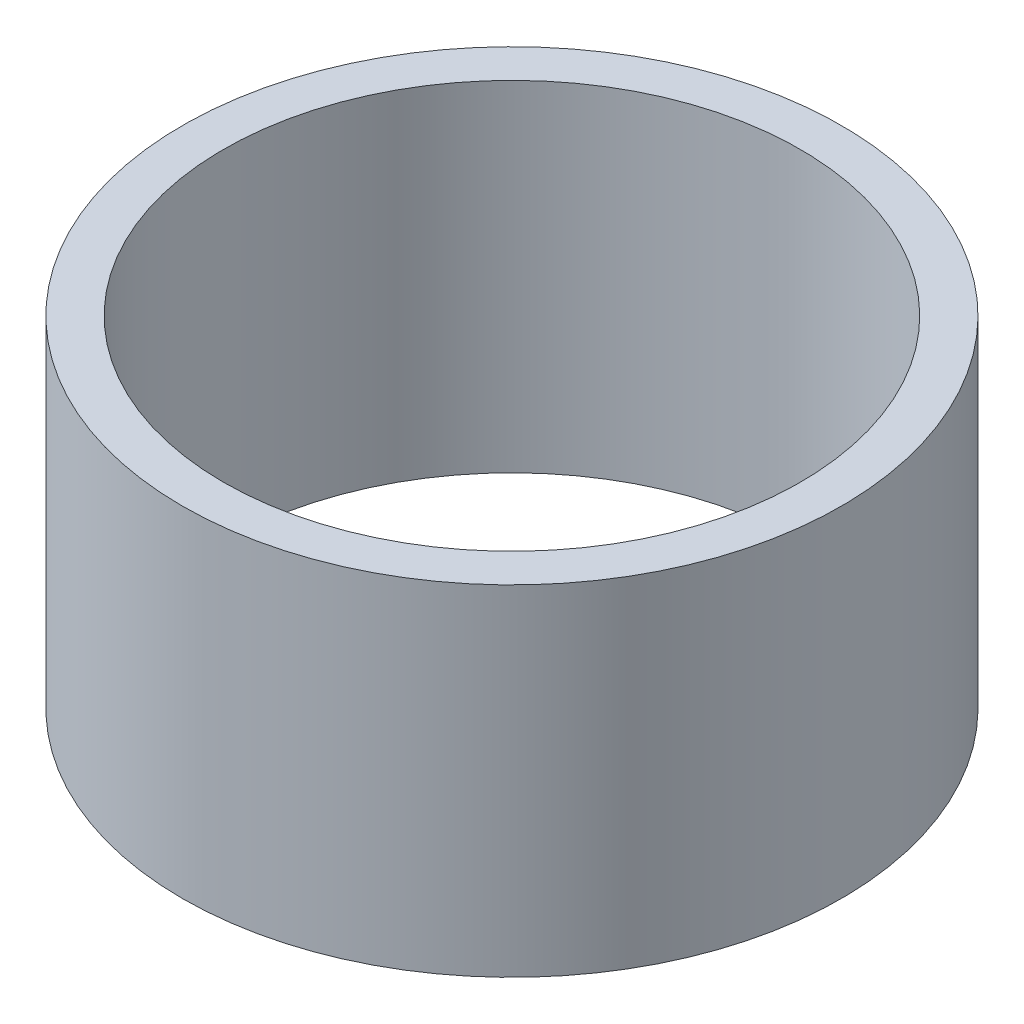
SolidWorks part; units mm, degrees
ref_plane "Front Plane" through (0, 0, 0) normal (0, 0, 1) x (1, 0, 0)
ref_plane "Top Plane" through (0, 0, 0) normal (0, 1, 0) x (1, 0, 0)
ref_plane "Right Plane" through (0, 0, 0) normal (1, 0, 0) x (0, 0, -1)
sketch "Sketch1" plane through (0, 0, 0) normal (0, 1, 0) x (1, 0, 0)
  circle A0 centre (0, 0) radius 32
  circle A1 centre (0, 0) radius 28
  dimension "D1" = 64
  dimension "D2" = 4
extrude "Boss-Extrude1" add sketch "Sketch1" along normal blind 33
